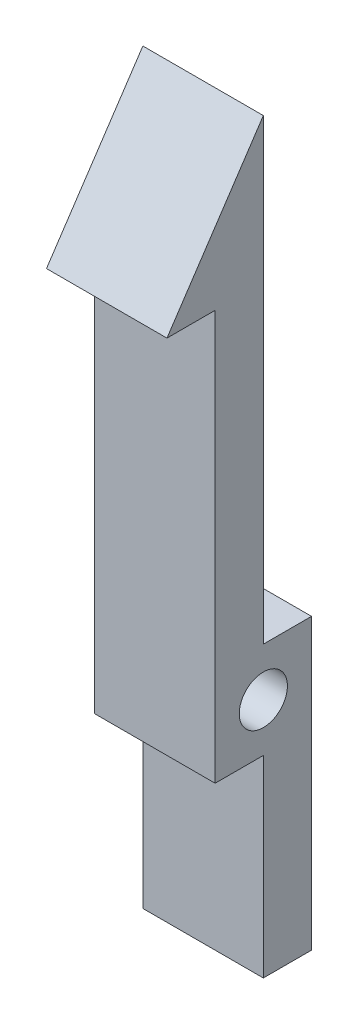
SolidWorks part; units mm, degrees
ref_plane "Ebene vorne" through (0, 0, 0) normal (0, 0, 1) x (1, 0, 0)
ref_plane "Ebene oben" through (0, 0, 0) normal (0, 1, 0) x (1, 0, 0)
ref_plane "Ebene rechts" through (0, 0, 0) normal (1, 0, 0) x (0, 0, -1)
sketch "Skizze1" plane through (0, 0, 0) normal (1, 0, 0) x (0, 0, -1)
  line L0 (0, 21) -> (-4, 15)
  line L1 (-4, 15) -> (-2, 15)
  line L2 (-2, 15) -> (-2, -2)
  line L3 (0, 2) -> (0, 21)
  line L4 (0, 2) -> (0, -2) construction
  line L5 (-2, -2) -> (0, -2)
  line L6 (0, -2) -> (0, -10)
  line L7 (0, -10) -> (2, -10)
  line L8 (2, -10) -> (2, 2)
  line L9 (2, 2) -> (0, 2)
  circle A0 centre (0, 0) radius 1
  dimension "D3" = 2
  dimension "D1" = 2
  dimension "D2" = 2
  dimension "D4" = 2
  dimension "D5" = 15
  dimension "D6" = 6
  dimension "D7" = 10
extrude "Linear austragen1" add sketch "Skizze1" against normal mid plane 5
